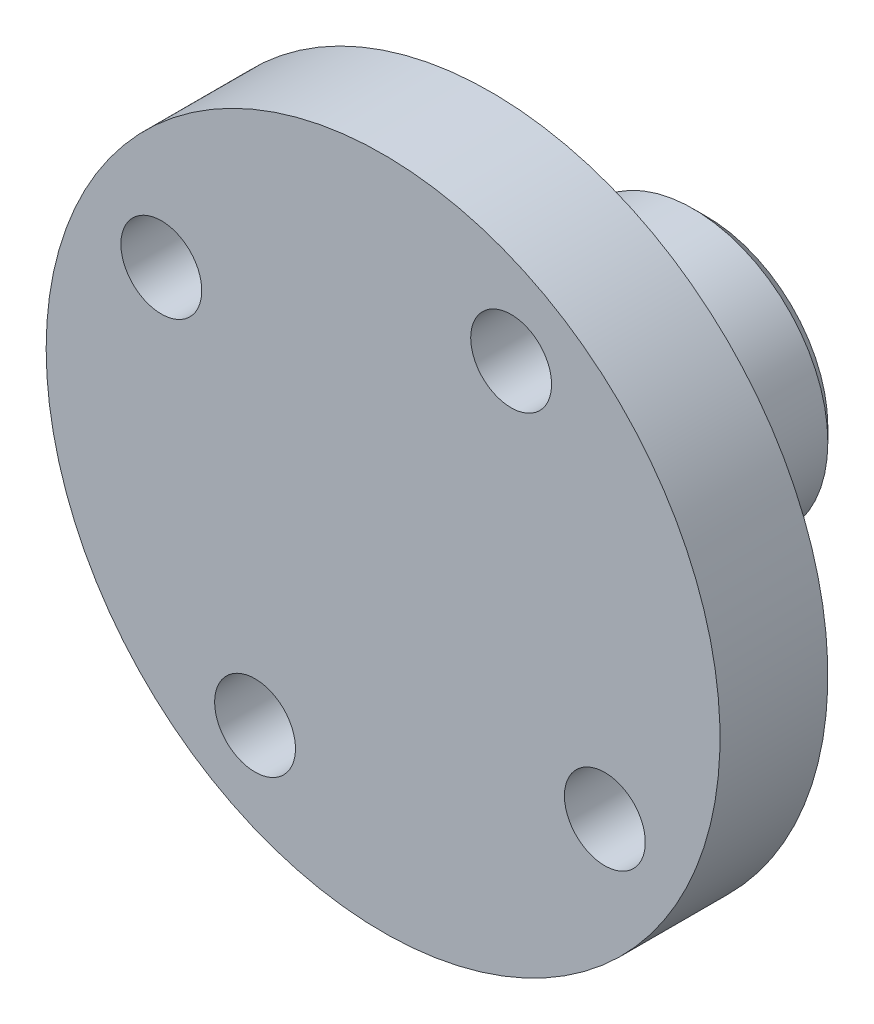
SolidWorks part; units mm, degrees
material "5052-H32"
ref_plane "Front Plane" through (0, 0, 0) normal (0, 0, 1) x (1, 0, 0)
ref_plane "Top Plane" through (0, 0, 0) normal (0, 1, 0) x (1, 0, 0)
ref_plane "Right Plane" through (0, 0, 0) normal (1, 0, 0) x (0, 0, -1)
sketch "Sketch1" plane through (0, 0, 0) normal (0, 1, 0) x (1, 0, 0)
  line L0 (0, 0) -> (0, -17.4703) construction
  line L1 (0, 0) -> (0, 4)
  line L2 (4, 12) -> (4, 4)
  line L3 (4, 4) -> (0, 4)
  line L4 (4, 12) -> (5, 12)
  line L5 (5, 12) -> (5, 4)
  line L6 (5, 4) -> (12.5, 4)
  line L7 (12.5, 4) -> (12.5, 0)
  line L8 (12.5, 0) -> (0, 0)
  line L9 (-4, 12) -> (-4, 4) construction
  line L10 (-5, 12) -> (-5, 4) construction
  line L11 (-12.5, 4) -> (-12.5, 0) construction
  dimension "D1" = 8
  dimension "D2" = 10
  dimension "D3" = 4
  dimension "D4" = 25
  dimension "D5" = 8
revolve "Revolve1" add sketch "Sketch1" angle 360 about L0
sketch "Sketch13" plane through (0, 0, -4) normal (0, 0, -1) x (-1, 0, 0)
  line L0 (0, 0) -> (9.5, 0) construction
  line L1 (-8.2272, -4.75) -> (4.75, -8.2272) construction
  line L2 (-8.2272, -4.75) -> (-4.75, 8.2272) construction
  line L3 (-4.75, 8.2272) -> (8.2272, 4.75) construction
  line L4 (4.75, -8.2272) -> (8.2272, 4.75) construction
  line L5 (-8.2272, -4.75) -> (8.2272, 4.75) construction
  line L6 (-4.75, 8.2272) -> (4.75, -8.2272) construction
  circle A0 centre (0, 0) radius 9.5 construction
  circle A1 centre (-4.75, 8.2272) radius 1.5
  circle A2 centre (-8.2272, -4.75) radius 1.5
  circle A3 centre (4.75, -8.2272) radius 1.5
  circle A4 centre (8.2272, 4.75) radius 1.5
  point P6 (0, 0)
  dimension "D1" = 19
  dimension "D3" = 3
  dimension "D2" = 30
sketch "Sketch5" plane through (0, 0, 0) normal (1, 0, 0) x (0, 0, -1)
  line L0 (4, 0) -> (12, 0) construction
  circle A0 centre (8, 0) radius 1.5
  dimension "D1" = 3
ref_plane "平面1" through (5, 0, 0) normal (1, 0, 0) x (0, 0, -1)
sketch "草圖7" plane through (5, 0, 0) normal (1, 0, 0) x (0, 0, -1)
  line L0 (0, 0) -> (8, 0) construction
  circle A0 centre (8, 0) radius 1.5
  dimension "D1" = 3
extrude "Cut-Extrude1" cut sketch "Sketch13" against normal up to next
extrude "Cut-Extrude2" cut sketch "Sketch5" against normal through all both and the other way through all
chamfer "Chamfer1" distance 0.5 angle 45 1 edges at (-5, 0, -12)
